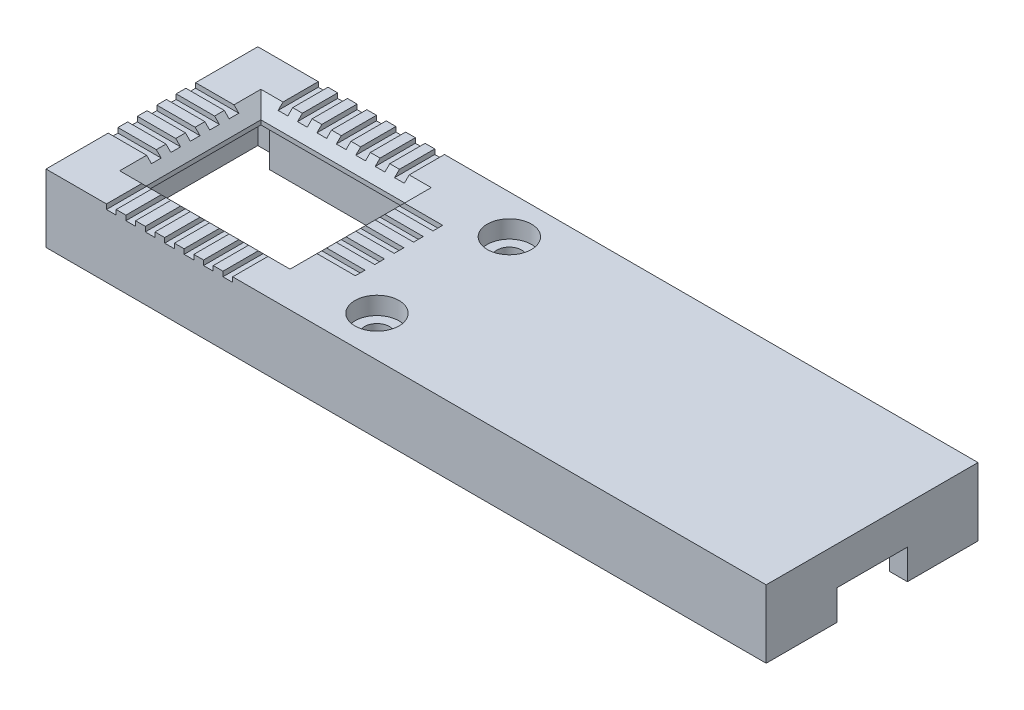
SolidWorks part; units mm, degrees
ref_plane "Front Plane" through (0, 0, 0) normal (0, 0, 1) x (1, 0, 0)
ref_plane "Top Plane" through (0, 0, 0) normal (0, 1, 0) x (1, 0, 0)
ref_plane "Right Plane" through (0, 0, 0) normal (1, 0, 0) x (0, 0, -1)
sketch "Sketch2" plane through (0, 0, 0) normal (0, 1, 0) x (1, 0, 0)
  line L0 (40.8, -12) -> (-40.8, -12)
  line L1 (38.8, -10) -> (-38.8, -10)
  line L2 (38.8, -10) -> (38.8, 10)
  line L3 (38.8, 10) -> (-38.8, 10)
  line L4 (-38.8, -10) -> (-38.8, 10)
  line L5 (38.8, -10) -> (-38.8, 10) construction
  line L6 (38.8, 10) -> (-38.8, -10) construction
  line L11 (-40.8, -12) -> (-40.8, 12)
  line L12 (40.8, 12) -> (-40.8, 12)
  line L13 (40.8, -12) -> (40.8, 12)
  point P0 (0, 0)
  point P6 (0, 0)
  dimension "D2" = 77.6
  dimension "D3" = 20
  dimension "D1" = 2
extrude "Boss-Extrude1" add sketch "Sketch2" along normal blind 7.7
sketch "Sketch3" plane through (0, 7.7, 0) normal (0, 1, 0) x (1, 0, 0)
  line L0 (38.8, 10) -> (-38.8, 10) construction
  line L1 (38.8, 10) -> (-38.8, 10)
  line L2 (-38.8, -10) -> (38.8, -10) construction
  line L3 (38.8, -10) -> (38.8, 10) construction
  line L4 (-38.8, 10) -> (-38.8, -10) construction
  line L5 (-38.8, -10) -> (38.8, -10)
  line L6 (38.8, -10) -> (38.8, 10)
  line L7 (-38.8, 10) -> (-38.8, -10)
extrude "Boss-Extrude2" add sketch "Sketch3" against normal blind 2
sketch "Sketch4" plane through (0, 7.7, 0) normal (0, 1, 0) x (1, 0, 0)
  line L0 (-38.8, 10) -> (-38.8, -10) construction
  line L1 (-34.95, -6.5) -> (-18.65, -6.5)
  line L2 (-34.95, -6.5) -> (-34.95, 6.5)
  line L3 (-34.95, 6.5) -> (-18.65, 6.5)
  line L4 (-18.65, -6.5) -> (-18.65, 6.5)
  line L5 (-34.95, -6.5) -> (-18.65, 6.5) construction
  line L6 (-34.95, 6.5) -> (-18.65, -6.5) construction
  point P0 (-26.8, 0)
  point P5 (0, 0)
  point P6 (0, 0)
  point P7 (0, 0)
  point P9 (0, 0)
  dimension "D1" = 16.3
  dimension "D2" = 13
  dimension "D3" = 3.85
extrude "Cut-Extrude1" cut sketch "Sketch4" against normal through all
sketch "Sketch5" plane through (40.8, 0, 0) normal (1, 0, 0) x (0, 0, -1)
  line L1 (4, -3.4) -> (-4, -3.4)
  line L2 (4, -3.4) -> (4, 3.4)
  line L3 (4, 3.4) -> (-4, 3.4)
  line L4 (-4, -3.4) -> (-4, 3.4)
  line L5 (4, -3.4) -> (-4, 3.4) construction
  line L6 (4, 3.4) -> (-4, -3.4) construction
  line L7 (-12, 0) -> (12, 0) construction
  point P0 (0, 0)
  point P5 (0, 0)
  point P8 (0, 0)
  dimension "D1" = 8
  dimension "D2" = 6.8
extrude "Cut-Extrude2" cut sketch "Sketch5" against normal up to next
sketch "Sketch6" plane through (0, 5.7, 0) normal (0, -1, 0) x (1, 0, 0)
  line L0 (-38.8, 10) -> (38.8, 10) construction
  line L1 (-34.95, 10) -> (-18.65, 10)
  line L2 (-34.95, 10) -> (-34.95, 7.5)
  line L3 (-34.95, 7.5) -> (-18.65, 7.5)
  line L4 (-18.65, 10) -> (-18.65, 7.5)
  line L5 (38.8, -10) -> (-38.8, -10) construction
  line L6 (-34.95, -10) -> (-18.65, -10)
  line L7 (-34.95, -10) -> (-34.95, -7.5)
  line L8 (-34.95, -7.5) -> (-18.65, -7.5)
  line L9 (-18.65, -10) -> (-18.65, -7.5)
  line L10 (-18.65, 6.5) -> (-18.65, -6.5) construction
  line L11 (38.8, 10) -> (22.5, 10)
  line L12 (38.8, 10) -> (38.8, 7.5)
  line L13 (38.8, 7.5) -> (22.5, 7.5)
  line L14 (22.5, 10) -> (22.5, 7.5)
  line L15 (38.8, -10) -> (33.8, -10)
  line L16 (38.8, -10) -> (38.8, -7.5)
  line L17 (38.8, -7.5) -> (33.8, -7.5)
  line L18 (33.8, -10) -> (33.8, -7.5)
  line L19 (-34.95, -6.5) -> (-34.95, 6.5) construction
  point P26 (-34.95, 8.75)
  point P27 (-26.8, 7.5)
  dimension "D1" = 2.5
  dimension "D2" = 5
extrude "Boss-Extrude3" add sketch "Sketch6" along normal offset from surface (4.9 mm away) 0.8 up to face at (13.2667, 0, 0)
sketch "Sketch8" plane through (0, 7.7, 0) normal (0, 1, 0) x (1, 0, 0)
  line L0 (33.8, 10) -> (-18.65, 10) construction
  line L1 (-38.8, 10) -> (-38.8, -10) construction
  circle A0 centre (-7.9, 7.6) radius 2.5
  circle A1 centre (-7.9, -7.4) radius 2.5
  dimension "D2" = 5
  dimension "D1" = 15
  dimension "D3" = 2.4
  dimension "D4" = 30.9
extrude "Cut-Extrude3" cut sketch "Sketch8" against normal blind 2
sketch "Sketch9" plane through (0, 5.7, 0) normal (0, -1, 0) x (1, 0, 0)
  line L0 (-18.65, 10) -> (22.5, 10) construction
  line L2 (-4.15, 4.8) -> (-4.15, 10)
  line L3 (-4.15, 10) -> (-11.65, 10)
  line L4 (-11.65, 4.8) -> (-11.65, 10)
  line L5 (-4.15, 4.8) -> (-11.65, 10) construction
  line L6 (-4.15, 10) -> (-11.65, 4.8) construction
  line L7 (38.8, -10) -> (-38.8, -10) construction
  line L9 (-4.15, -5.2) -> (-4.15, -10)
  line L10 (-4.15, -10) -> (-11.65, -10)
  line L11 (-11.65, -5.2) -> (-11.65, -10)
  line L12 (-4.15, -5.2) -> (-11.65, -10) construction
  line L13 (-4.15, -10) -> (-11.65, -5.2) construction
  line L14 (-11.65, -5.2) -> (-11.65, 4.8)
  line L15 (-4.15, 4.8) -> (-4.15, -5.2)
  circle A0 centre (-7.9, 7.4) radius 1.4
  circle A1 centre (-7.9, -7.6) radius 1.4
  point P0 (-7.9, 7.4)
  point P8 (-7.9, -7.6)
  point P20 (0, 0)
  dimension "D2" = 2.8
  dimension "D1" = 7.5
extrude "Boss-Extrude4" add sketch "Sketch9" along normal blind 2
sketch "Sketch10" plane through (0, 3.7, 0) normal (0, -1, 0) x (1, 0, 0)
  line L0 (-10.3, 7.4) -> (-10.3, 10)
  line L1 (-4.15, 10) -> (-11.65, 10) construction
  line L2 (-5.5, 7.4) -> (-5.5, 10)
  line L3 (-38.8, 10) -> (38.8, 10) construction
  line L4 (-5.5, 10) -> (-10.3, 10)
  line L5 (-10.3, -7.6) -> (-10.3, -10)
  line L6 (38.8, -10) -> (-38.8, -10) construction
  line L7 (-5.5, -7.6) -> (-5.5, -10)
  line L8 (-11.65, -10) -> (-4.15, -10) construction
  line L9 (-5.5, -10) -> (-10.3, -10)
  arc A0 (-10.3, 7.4) -> (-5.5, 7.4) centre (-7.9, 7.4) ccw
  arc A1 (-5.5, -7.6) -> (-10.3, -7.6) centre (-7.9, -7.6) ccw
  circle A2 centre (-7.9, 7.4) radius 1.4 construction
  circle A3 centre (-7.9, 7.4) radius 1.4
  circle A4 centre (-7.9, -7.6) radius 1.4 construction
  circle A5 centre (-7.9, -7.6) radius 1.4
  dimension "D1" = 4.8
extrude "Boss-Extrude5" add sketch "Sketch10" along normal up to surface (2.9 mm away) up to face at (-26.8, 0.8, 8.75)
chamfer "Chamfer1" distance 1.5 angle 45 4 edges at (-34.95, 7.7, 0) (-26.8, 7.7, 6.5) (-26.8, 7.7, -6.5) (-18.65, 7.7, 0)
sketch "Sketch11" plane through (0, 0, 12) normal (0, 0, 1) x (1, 0, 0)
  line L0 (-40.8, 7.7) -> (40.8, 7.7) construction
  line L1 (-27.35, 8.25) -> (-26.25, 8.25)
  line L2 (-27.35, 8.25) -> (-27.35, 7.15)
  line L3 (-27.35, 7.15) -> (-26.25, 7.15)
  line L4 (-26.25, 8.25) -> (-26.25, 7.15)
  line L5 (-27.35, 8.25) -> (-26.25, 7.15) construction
  line L6 (-27.35, 7.15) -> (-26.25, 8.25) construction
  line L7 (-17.15, 7.7) -> (-36.45, 7.7) construction
  point P0 (-26.8, 7.7)
  point P9 (0, 0)
  dimension "D1" = 1.1
extrude "Cut-Extrude4" cut sketch "Sketch11" against normal through all
pattern_linear "LPattern1" count 4 spacing 2.2 along (1, 0, 0) of "Cut-Extrude4"
pattern_linear "LPattern2" count 4 spacing 2.2 along (-1, 0, 0) of "Cut-Extrude4"
sketch "Sketch12" plane through (-40.8, 0, 0) normal (-1, 0, 0) x (0, 0, 1)
  line L0 (-12, 7.7) -> (12, 7.7) construction
  line L1 (-0.55, 8.25) -> (0.55, 8.25)
  line L2 (-0.55, 8.25) -> (-0.55, 7.15)
  line L3 (-0.55, 7.15) -> (0.55, 7.15)
  line L4 (0.55, 8.25) -> (0.55, 7.15)
  line L5 (-0.55, 8.25) -> (0.55, 7.15) construction
  line L6 (-0.55, 7.15) -> (0.55, 8.25) construction
  point P0 (0, 7.7)
  dimension "D1" = 1.1
extrude "Cut-Extrude5" cut sketch "Sketch12" against normal blind 28
pattern_linear "LPattern3" count 3 spacing 2.2 along (0, 0, 1) of "Cut-Extrude5"
pattern_linear "LPattern4" count 3 spacing 2.2 along (0, 0, -1) of "Cut-Extrude5"
